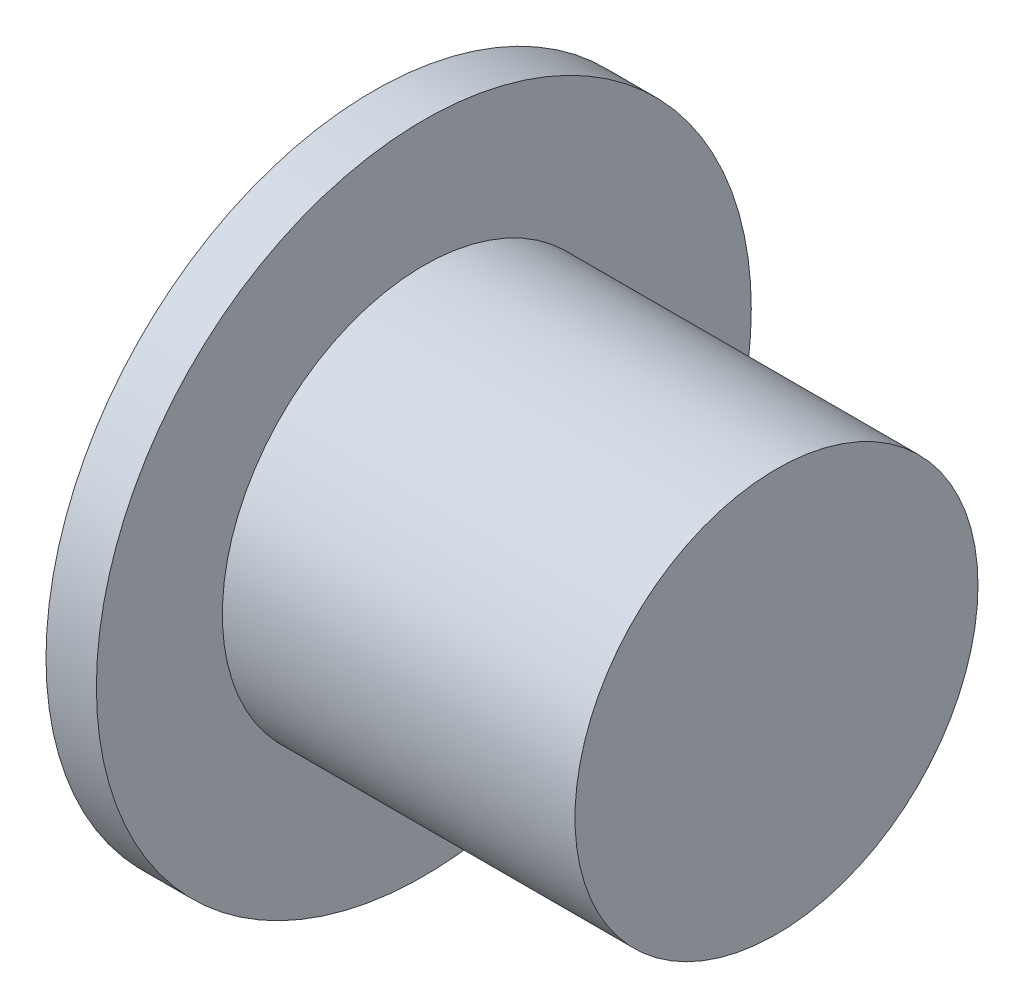
SolidWorks part; units mm, degrees
ref_plane "Front Plane" through (0, 0, 0) normal (0, 0, 1) x (1, 0, 0)
ref_plane "Top Plane" through (0, 0, 0) normal (0, 1, 0) x (1, 0, 0)
ref_plane "Right Plane" through (0, 0, 0) normal (1, 0, 0) x (0, 0, -1)
sketch "Sketch2" plane through (0, 0, 0) normal (1, 0, 0) x (0, 0, -1)
  circle A0 centre (0, 0) radius 4
  dimension "D1" = 8
extrude "Boss-Extrude1" add sketch "Sketch2" against normal blind 7
sketch "Sketch3" plane through (-7, 0, 0) normal (-1, 0, 0) x (0, 0, 1)
  circle A0 centre (0, 0) radius 6.5
  circle A1 centre (0, 0) radius 4 construction
  dimension "D1" = 13
extrude "Boss-Extrude2" add sketch "Sketch3" along normal blind 1
